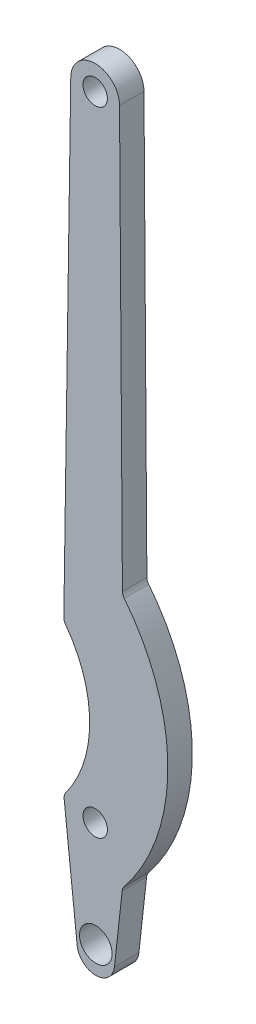
SolidWorks part; units mm, degrees
material "7075-O (SS)"
ref_plane "前视基准面" through (0, 0, 0) normal (0, 0, 1) x (1, 0, 0)
ref_plane "上视基准面" through (0, 0, 0) normal (0, 1, 0) x (1, 0, 0)
ref_plane "右视基准面" through (0, 0, 0) normal (1, 0, 0) x (0, 0, -1)
sketch "草图1" plane through (0, 0, 0) normal (0, 0, 1) x (1, 0, 0)
  line L0 (-2.2867, -0.2467) -> (-3.8839, 14.5565)
  line L1 (2.2859, -0.254) -> (3.2372, 8.3074)
  line L2 (-3.9266, 14.9522) -> (-3.9266, 33.4209) construction
  line L3 (-3.9266, 24.1866) -> (-15.7472, 24.1866) construction
  line L4 (3.2671, 40.1242) -> (2.9117, 91.5814)
  line L5 (-3.9215, 33.7671) -> (-3.0697, 91.6048)
  line L6 (-3.8547, 14.9257) -> (-0.0738, 13.8996) construction
  arc A1 (-2.2867, -0.2467) -> (2.2859, -0.254) centre (0, 0) ccw
  arc A4 (-3.6932, 15.259) -> (-3.7232, 33.1545) centre (-15.7472, 24.1866) ccw
  arc A5 (3.4503, 8.8218) -> (3.485, 39.508) centre (-15.7472, 24.1866) ccw
  arc A8 (2.9117, 91.5814) -> (-3.0697, 91.6048) centre (-0.0791, 91.5607) ccw
  circle A9 centre (-0.0791, 91.5607) radius 1.5
  arc A10 (-3.6932, 15.259) -> (-3.8839, 14.5565) centre (-2.8896, 14.6638) ccw
  arc A11 (3.4503, 8.8218) -> (3.2372, 8.3074) centre (4.2311, 8.1969) ccw
  arc A12 (3.2671, 40.1242) -> (3.485, 39.508) centre (4.2671, 40.1311) ccw
  arc A13 (-3.9215, 33.7671) -> (-3.7232, 33.1545) centre (-2.9216, 33.7523) ccw
  circle A15 centre (-0.0738, 13.8996) radius 1.5
  circle A16 centre (0, 1) radius 2
  point P20 (3.2695, 8.5986)
  point P23 (3.2695, 39.7746)
  dimension "D1" = 1
  dimension "D2" = 2.3
  dimension "D4" = 15
  dimension "D5" = 24.589
  dimension "D6" = 3
  dimension "D7" = 4
  dimension "D3" = 1.24
  dimension "D8" = 1
extrude "凸台-拉伸1" add sketch "草图1" along normal blind 3
